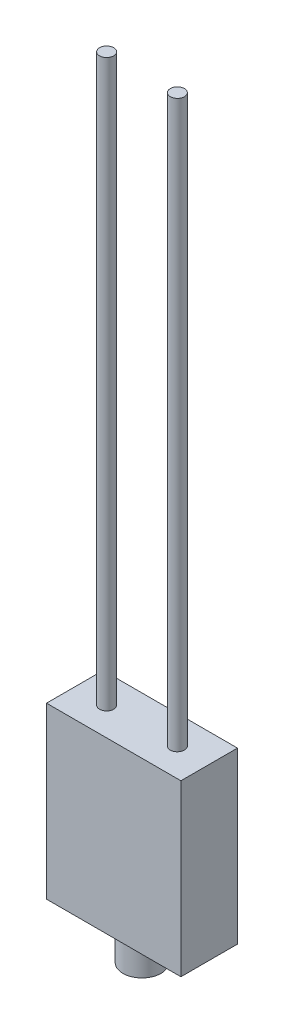
SolidWorks part; units mm, degrees
ref_plane "前视基准面" through (0, 0, 0) normal (0, 0, 1) x (1, 0, 0)
ref_plane "上视基准面" through (0, 0, 0) normal (0, 1, 0) x (1, 0, 0)
ref_plane "右视基准面" through (0, 0, 0) normal (1, 0, 0) x (0, 0, -1)
sketch "草图1" plane through (0, 0, 0) normal (0, 1, 0) x (1, 0, 0)
  line L5 (-9.5, 4) -> (9.5, 4)
  line L6 (-9.5, 4) -> (-9.5, -4)
  line L7 (-9.5, -4) -> (9.5, -4)
  line L8 (9.5, 4) -> (9.5, -4)
  line L9 (0, -4) -> (0, 4) construction
  line L10 (-9.5, 0) -> (9.5, 0) construction
  point P0 (0, 0)
  dimension "D1" = 8
  dimension "D2" = 19
extrude "凸台-拉伸1" add sketch "草图1" along normal blind 24
sketch "草图2" plane through (0, 24, 0) normal (0, 1, 0) x (1, 0, 0)
  line L0 (0, 13.313) -> (0, -7.37) construction
  line L1 (-7.0483, 0) -> (8.7753, 0) construction
  circle A0 centre (5, 0) radius 1
  circle A1 centre (-5, 0) radius 1
  dimension "D1" = 2
  dimension "D2" = 5
extrude "凸台-拉伸2" add sketch "草图2" along normal blind 80
sketch "草图3" plane through (0, 0, 0) normal (0, -1, 0) x (1, 0, 0)
  circle A0 centre (0, 0) radius 2.6861
extrude "凸台-拉伸3" add sketch "草图3" along normal blind 5
